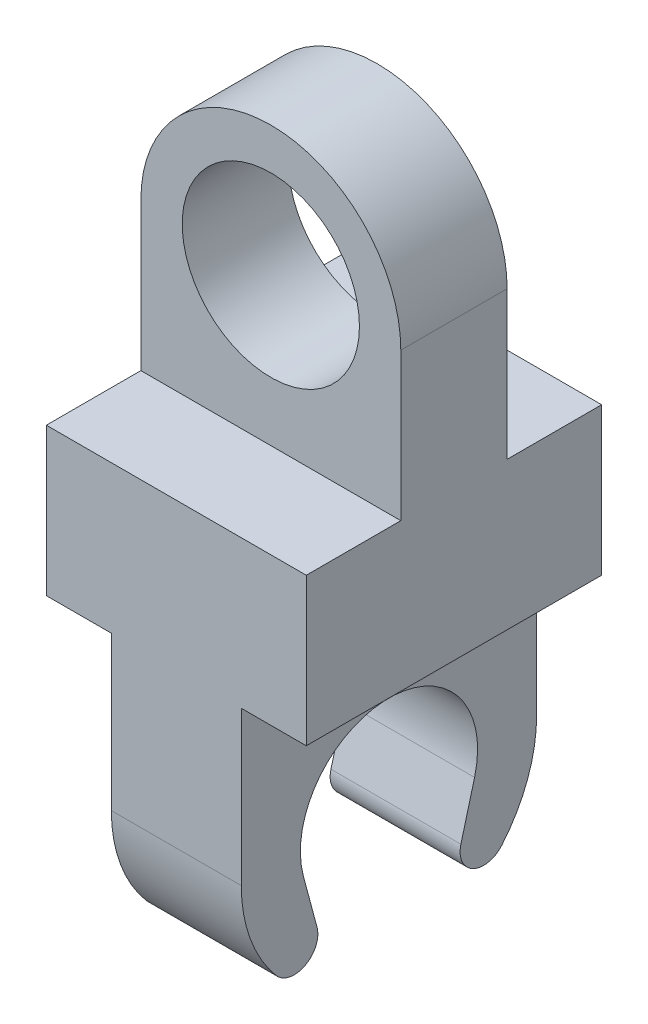
SolidWorks part; units mm, degrees
material "ABS"
ref_plane "Front Plane" through (0, 0, 0) normal (1, 0, 0) x (0, 1, 0)
ref_plane "Top Plane" through (0, 0, 0) normal (0, 0, 1) x (0, 1, 0)
ref_plane "Right Plane" through (0, 0, 0) normal (0, 1, 0) x (-1, 0, 0)
sketch "Sketch1" plane through (0, 0, 0) normal (0, 0, 1) x (0, 1, 0)
  line L0 (0, 0) -> (25, 0) construction
  line L1 (0, 22) -> (25, 22)
  line L2 (0, -22) -> (25, -22)
  line L3 (0, 22) -> (0, -22)
  arc A1 (25, -22) -> (25, 22) centre (25, 0) ccw
  point P3 (12.5, 0)
  point P11 (0, 18.7684)
  dimension "D1" = 22
  dimension "D2" = 25
  dimension "D3" = 44
extrude "Boss-Extrude2" add sketch "Sketch1" along normal blind 9
sketch "Sketch2" plane through (0, 0, 0) normal (1, 0, 0) x (0, 1, 0)
  line L0 (0, 9) -> (0, 25)
  line L1 (0, 25) -> (-25, 25)
  line L2 (-25, 25) -> (-25, 0)
  line L3 (-25, 0) -> (0, 0)
  line L9 (0, 0) -> (25, 0)
  line L10 (25, 0) -> (25, 9)
  line L11 (25, 9) -> (0, 9)
  line L12 (0, 9) -> (0, 0)
  line L13 (0, 0) -> (25, 0)
  line L14 (25, 0) -> (25, 9)
  line L15 (25, 9) -> (0, 9)
  dimension "D1" = 25
  dimension "D2" = 25
  dimension "D3" = 0
extrude "Boss-Extrude3" add sketch "Sketch2" along normal mid plane 44 contours L14 L15 L0 L1 L2 L3 L13
sketch "Sketch3" plane through (22, 0, 0) normal (1, 0, 0) x (0, 1, 0)
  line L0 (-25, 25) -> (-51, 25)
  line L1 (-54.8823, 14.4889) -> (-63.5218, 12.1739)
  line L4 (0, 0) -> (-52.6184, 0) construction
  line L5 (-36, 0) -> (-25, 0)
  line L6 (-25, 25) -> (-25, 0)
  line L8 (25, 9) -> (25, 0) construction
  arc A0 (-54.8823, 14.4889) -> (-36, 0) centre (-51, 0) cw
  arc A1 (-51, 25) -> (-67.1394, 19.0924) centre (-51, 0) ccw
  arc A2 (-63.5218, 12.1739) -> (-67.1394, 19.0924) centre (-64.5571, 16.0376) cw
  dimension "D1" = 15
  dimension "D3" = 50
  dimension "D4" = 15
  dimension "D5" = 76
  dimension "D2" = 4
extrude "Boss-Extrude5" add sketch "Sketch3" against normal blind 22 from offset 11 offset against normal yes
mirror "Mirror1" about plane through (0, 25, 0) normal (0, 0, 1) of bodies 105
sketch "Sketch4" plane through (0, 0, 9) normal (0, 0, 1) x (1, 0, 0)
  circle A0 centre (0, 25) radius 15
  dimension "D1" = 30
  dimension "D2" = 25
extrude "Cut-Extrude1" cut sketch "Sketch4" against normal blind 44
